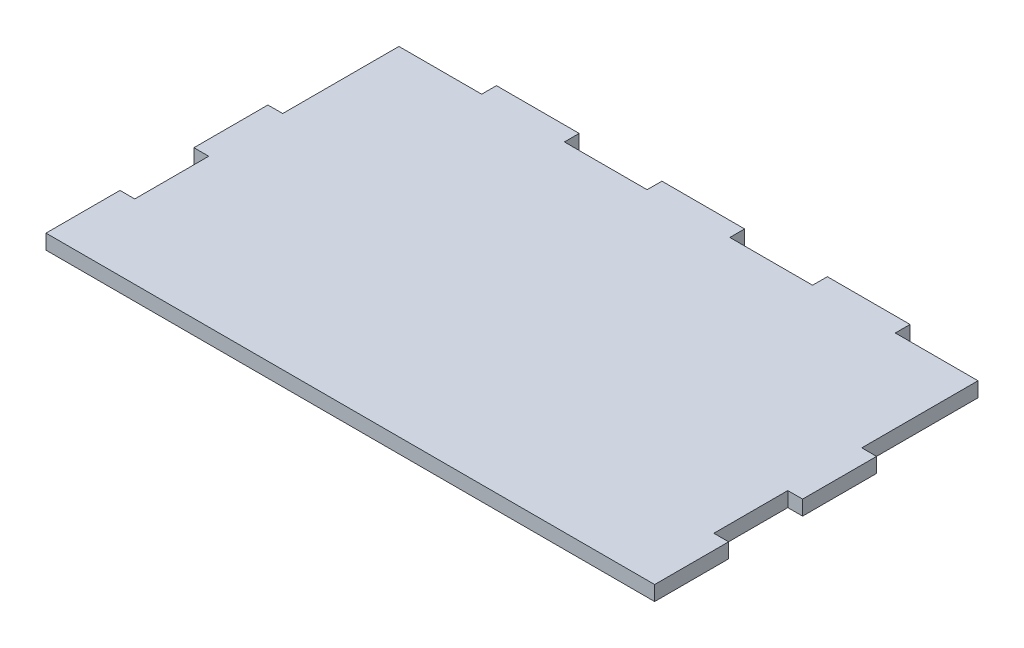
SolidWorks part; units mm, degrees
ref_plane "Front Plane" through (0, 0, 0) normal (0, 0, 1) x (1, 0, 0)
ref_plane "Top Plane" through (0, 0, 0) normal (0, 1, 0) x (1, 0, 0)
ref_plane "Right Plane" through (0, 0, 0) normal (1, 0, 0) x (0, 0, -1)
sketch "Sketch1" plane through (0, 0, 0) normal (0, 1, 0) x (1, 0, 0)
  line L0 (-1.75, 26.25) -> (-1.75, 35) construction
  line L1 (0, 0) -> (68.5, 0)
  line L2 (0, 0) -> (0, 40)
  line L3 (0, 40) -> (68.5, 40)
  line L4 (68.5, 0) -> (68.5, 40)
  line L5 (0, 0) -> (-1.75, 0)
  line L6 (0, 0) -> (0, 8.75)
  line L7 (0, 8.75) -> (-1.75, 8.75)
  line L8 (-1.75, 0) -> (-1.75, 8.75)
  line L9 (0, 17.5) -> (-1.75, 17.5)
  line L10 (0, 17.5) -> (0, 26.25)
  line L11 (0, 26.25) -> (-1.75, 26.25)
  line L12 (-1.75, 17.5) -> (-1.75, 26.25)
  line L13 (-1.75, 8.75) -> (-1.75, 17.5) construction
  line L14 (34.25, 0) -> (34.25, 40) construction
  line L15 (68.5, 26.25) -> (70.25, 26.25)
  line L16 (70.25, 17.5) -> (70.25, 26.25)
  line L17 (68.5, 17.5) -> (70.25, 17.5)
  line L18 (68.5, 17.5) -> (68.5, 26.25)
  line L19 (68.5, 8.75) -> (70.25, 8.75)
  line L20 (70.25, 0) -> (70.25, 8.75)
  line L21 (68.5, 0) -> (70.25, 0)
  line L22 (68.5, 0) -> (68.5, 8.75)
  line L23 (0, 41.75) -> (9.7857, 41.75) construction
  line L24 (29.3571, 41.75) -> (39.1429, 41.75)
  line L25 (9.7857, 41.75) -> (19.5714, 41.75)
  line L26 (9.7857, 41.75) -> (9.7857, 40)
  line L27 (9.7857, 40) -> (19.5714, 40)
  line L28 (19.5714, 41.75) -> (19.5714, 40)
  line L29 (29.3571, 41.75) -> (29.3571, 40)
  line L30 (29.3571, 40) -> (39.1429, 40)
  line L31 (39.1429, 41.75) -> (39.1429, 40)
  line L32 (19.5714, 41.75) -> (29.3571, 41.75) construction
  line L33 (48.9286, 41.75) -> (58.7143, 41.75)
  line L34 (48.9286, 41.75) -> (48.9286, 40)
  line L35 (48.9286, 40) -> (58.7143, 40)
  line L36 (58.7143, 41.75) -> (58.7143, 40)
  line L37 (39.1429, 41.75) -> (48.9286, 41.75) construction
  line L42 (58.7143, 41.75) -> (68.5, 41.75) construction
  line L45 (68.5, 41.75) -> (78.2857, 41.75) [skipped]
  line L46 (78.2857, 41.75) -> (78.2857, 40) [skipped]
  line L47 (68.5, 40) -> (78.2857, 40) [skipped]
  line L48 (68.5, 41.75) -> (68.5, 40) [skipped]
  dimension "D1" = 40
  dimension "D2" = 68.5
  dimension "D3" = 1.75
  dimension "D5" = 8.75
  dimension "D4" = 4
extrude "Boss-Extrude1" add sketch "Sketch1" along normal blind 1.75 contours L1 L4 L3 L2 | L12 L9 L2 L11 | L8 L5 L2 L7 | L28 L25 L26 L3 | L31 L24 L29 L3 | L36 L33 L34 L3 | L4 L17 L16 L15 | L4 L21 L20 L19
equation "\"D2@Sketch1\"=\"thick\"*2 + 65mm"
equation "\"D3@Sketch1\"=\"thick\"+\"veneer_thickness\""
equation "\"D1@Boss-Extrude1\"=\"thick\"+\"veneer_thickness\""
equation "\"veneer_thickness\"= 0.0mm"
equation "\"thick\"= 1.75mm"
